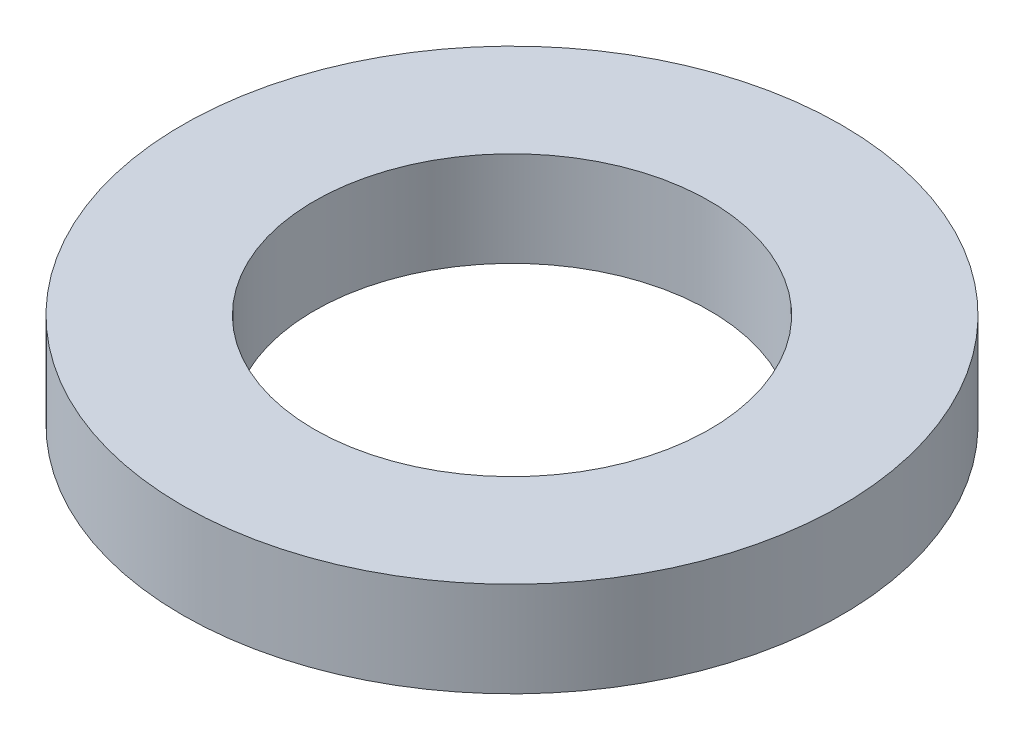
SolidWorks part; units mm, degrees
ref_plane "Plano frontal" through (0, 0, 0) normal (0, 0, 1) x (1, 0, 0)
ref_plane "Plano superior" through (0, 0, 0) normal (0, 1, 0) x (1, 0, 0)
ref_plane "Plano direito" through (0, 0, 0) normal (1, 0, 0) x (0, 0, -1)
sketch "Sketch1" plane through (0, 0, 0) normal (0, 1, 0) x (1, 0, 0)
  circle A0 centre (0, 0) radius 3.75
  circle A1 centre (0, 0) radius 6.25
  dimension "D1" = 7.5
  dimension "D2" = 12.5
extrude "Boss-Extrude1" add sketch "Sketch1" along normal mid plane 1.8
